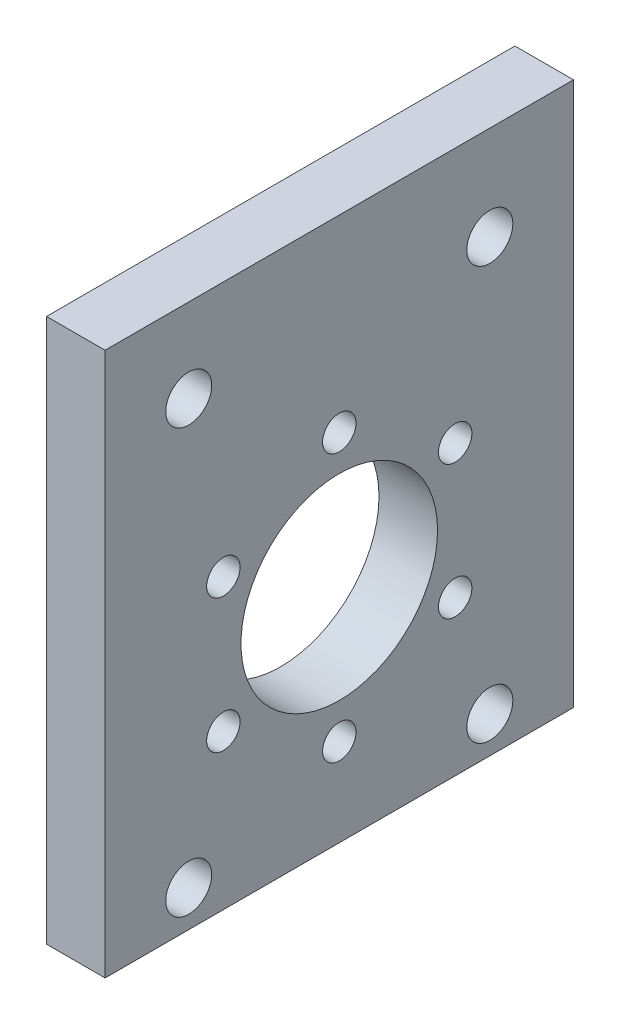
SolidWorks part; units mm, degrees
ref_plane "Front Plane" through (0, 0, 0) normal (0, 0, 1) x (1, 0, 0)
ref_plane "Top Plane" through (0, 0, 0) normal (0, 1, 0) x (1, 0, 0)
ref_plane "Right Plane" through (0, 0, 0) normal (1, 0, 0) x (0, 0, -1)
sketch "Sketch1" plane through (0, 0, 0) normal (1, 0, 0) x (0, 0, -1)
  line L1 (0, 0) -> (56, 0)
  line L2 (0, 0) -> (0, -65)
  line L3 (0, -65) -> (56, -65)
  line L4 (56, 0) -> (56, -65)
  dimension "D1" = 56
  dimension "D2" = 65
extrude "Boss-Extrude1" add sketch "Sketch1" along normal blind 7
sketch "Sketch2" plane through (7, 0, 0) normal (1, 0, 0) x (0, 0, -1)
  line L0 (56, 0) -> (0, 0) construction
  line L1 (56, 0) -> (0, 0) construction
  circle A0 centre (28, -38.52) radius 11.75
  point P5 (28, 0)
  dimension "D1" = 23.5
  dimension "D2" = 38.52
extrude "Cut-Extrude1" cut sketch "Sketch2" against normal through all
sketch "Sketch3" plane through (0, 0, 0) normal (-1, 0, 0) x (0, 0, 1)
  circle A0 centre (-28, -22.52) radius 1.25 construction
  circle A1 centre (-28, -22.52) radius 1.25 construction
  circle A2 centre (-41.8564, -30.52) radius 1.25 construction
  circle A3 centre (-41.8564, -30.52) radius 1.25 construction
  circle A4 centre (-14.1436, -46.52) radius 1.25 construction
  circle A5 centre (-14.1436, -46.52) radius 1.25 construction
  circle A6 centre (-28, -54.52) radius 1.25 construction
  circle A7 centre (-28, -54.52) radius 1.25 construction
  circle A8 centre (-41.8564, -46.52) radius 1.25 construction
  circle A9 centre (-41.8564, -46.52) radius 1.25 construction
  circle A10 centre (-14.1436, -30.52) radius 1.25 construction
  circle A11 centre (-14.1436, -30.52) radius 1.25 construction
  circle A12 centre (-41.8564, -30.52) radius 2
  circle A13 centre (-28, -22.52) radius 2
  circle A14 centre (-14.1436, -30.52) radius 2
  circle A15 centre (-14.1436, -46.52) radius 2
  circle A16 centre (-28, -54.52) radius 2
  circle A17 centre (-41.8564, -46.52) radius 2
  dimension "D1" = 4
  dimension "D2" = 4
  dimension "D3" = 4
  dimension "D4" = 4
  dimension "D5" = 4
  dimension "D6" = 4
extrude "Cut-Extrude2" cut sketch "Sketch3" against normal through all
sketch "Sketch4" plane through (7, 0, 0) normal (1, 0, 0) x (0, 0, -1)
  circle A0 centre (10, -60.6477) radius 2.75 construction
  circle A1 centre (10, -60.6477) radius 2.75
  circle A2 centre (10, -9.9985) radius 2.75 construction
  circle A3 centre (10, -9.9985) radius 2.75
  circle A4 centre (46, -11.2567) radius 2.75 construction
  circle A5 centre (46, -11.2567) radius 2.75
  circle A6 centre (46, -60.6477) radius 2.75 construction
  circle A7 centre (46, -60.6477) radius 2.75
extrude "Cut-Extrude3" cut sketch "Sketch4" against normal through all
